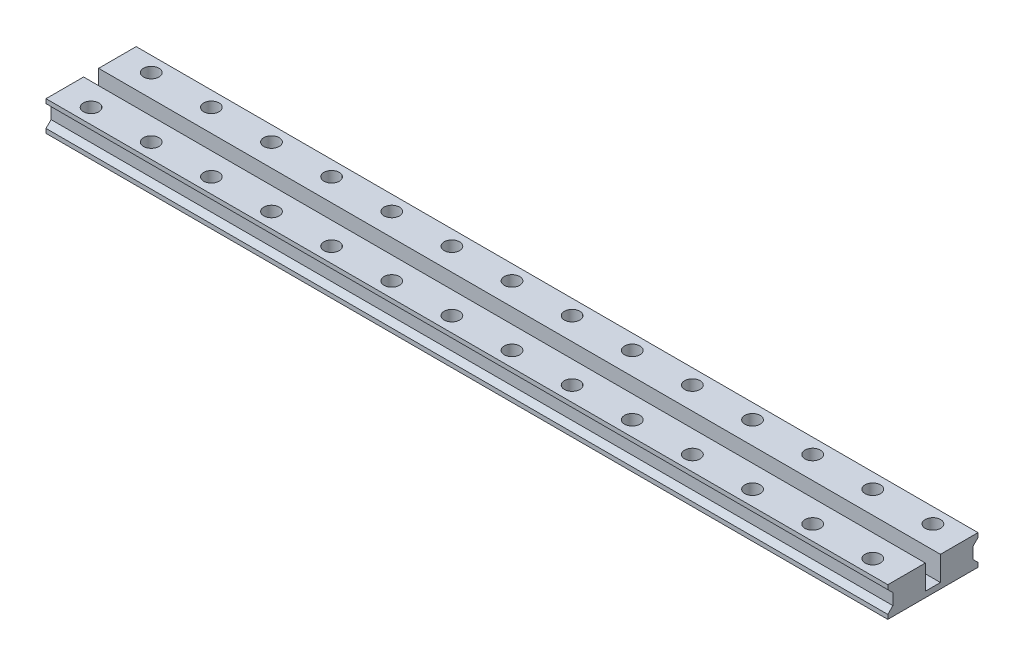
SolidWorks part; units mm, degrees
material "6061-O (SS)"
ref_plane "Front Plane" through (0, 0, 0) normal (0, 0, 1) x (1, 0, 0)
ref_plane "Top Plane" through (0, 0, 0) normal (0, 1, 0) x (1, 0, 0)
ref_plane "Right Plane" through (0, 0, 0) normal (1, 0, 0) x (0, 0, -1)
sketch "Sketch1" plane through (0, 0, 0) normal (0, 1, 0) x (1, 0, 0)
  line L1 (-112, -12) -> (112, -12)
  line L2 (-112, -12) -> (-112, 12)
  line L3 (-112, 12) -> (112, 12)
  line L4 (112, -12) -> (112, 12)
  line L5 (-112, -12) -> (112, 12) construction
  line L6 (-112, 12) -> (112, -12) construction
  point P0 (0, 0)
  dimension "D1" = 224
  dimension "D2" = 24
extrude "Boss-Extrude1" add sketch "Sketch1" along normal blind 8
sketch "Sketch2" plane through (0, 8, 0) normal (0, 1, 0) x (1, 0, 0)
  line L0 (-112, 8) -> (112, 8) construction
  line L1 (-112, 12) -> (-112, -12) construction
  line L2 (112, -12) -> (112, 12) construction
  line L3 (-112, 0) -> (112, 0) construction
  circle A0 centre (-104, 8) radius 2.05
  circle A1 centre (-88, 8) radius 2.05
  circle A2 centre (-72, 8) radius 2.05
  circle A3 centre (-56, 8) radius 2.05
  circle A4 centre (-40, 8) radius 2.05
  circle A5 centre (-24, 8) radius 2.05
  circle A6 centre (-8, 8) radius 2.05
  circle A7 centre (8, 8) radius 2.05
  circle A8 centre (24, 8) radius 2.05
  circle A9 centre (40, 8) radius 2.05
  circle A10 centre (56, 8) radius 2.05
  circle A11 centre (72, 8) radius 2.05
  circle A12 centre (88, 8) radius 2.05
  circle A13 centre (104, 8) radius 2.05
  circle A14 centre (-88, -8) radius 2.05
  circle A15 centre (-72, -8) radius 2.05
  circle A16 centre (-56, -8) radius 2.05
  circle A17 centre (-40, -8) radius 2.05
  circle A18 centre (-24, -8) radius 2.05
  circle A19 centre (-8, -8) radius 2.05
  circle A20 centre (8, -8) radius 2.05
  circle A21 centre (24, -8) radius 2.05
  circle A22 centre (40, -8) radius 2.05
  circle A23 centre (56, -8) radius 2.05
  circle A24 centre (72, -8) radius 2.05
  circle A25 centre (88, -8) radius 2.05
  circle A26 centre (104, -8) radius 2.05
  circle A27 centre (-104, -8) radius 2.05
  point P64 (-83.6142, 8)
  dimension "D3" = 4.1
  dimension "D6" = 16
  dimension "D4" = 8
  dimension "D5" = 16
  dimension "D1" = 14
  dimension "D2" = 2
extrude "Cut-Extrude1" cut sketch "Sketch2" against normal through all
sketch "Sketch3" plane through (-112, 0, 0) normal (-1, 0, 0) x (0, 0, 1)
  line L0 (0, 0) -> (0, 8) construction
  line L1 (-12, 8) -> (12, 8) construction
  line L2 (-12, 4) -> (12, 4) construction
  line L3 (2, 1.5) -> (-2, 1.5)
  line L4 (2, 1.5) -> (2, 8)
  line L5 (2, 8) -> (-2, 8)
  line L6 (-2, 1.5) -> (-2, 8)
  line L7 (2, 1.5) -> (-2, 8) construction
  line L8 (2, 8) -> (-2, 1.5) construction
  line L9 (-12, 8) -> (-12, 0) construction
  line L10 (12, 8) -> (12, 0) construction
  line L11 (-12, 6.85) -> (-10.65, 5.5)
  line L12 (-10.65, 5.5) -> (-10.65, 2.5)
  line L13 (-12, 1.15) -> (-10.65, 2.5)
  line L14 (-12, 6.85) -> (-12, 1.15)
  line L15 (12, 6.85) -> (12, 1.15)
  line L16 (12, 1.15) -> (10.65, 2.5)
  line L17 (10.65, 5.5) -> (10.65, 2.5)
  line L18 (12, 6.85) -> (10.65, 5.5)
  point P5 (0, 4.75)
  point P20 (-10.65, 4)
  point P21 (10.65, 4)
  dimension "D1" = 4
  dimension "D2" = 6.5
  dimension "D3" = 3
  dimension "D4" = 45
  dimension "D5" = 1.35
extrude "Cut-Extrude2" cut sketch "Sketch3" against normal through all
